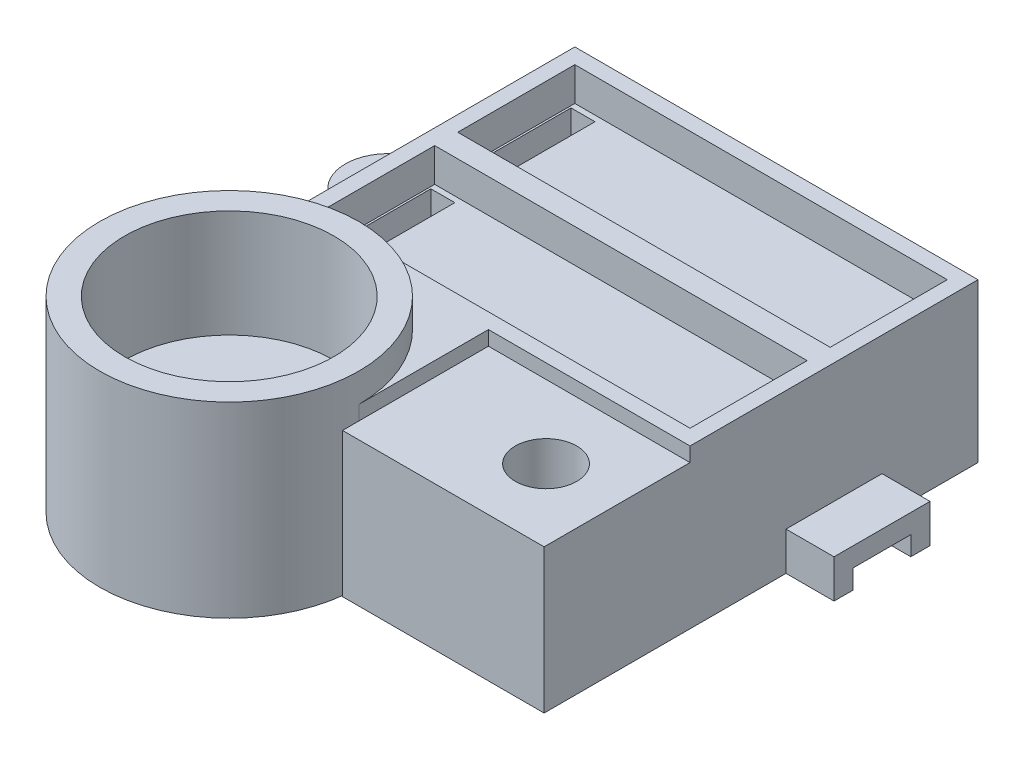
SolidWorks part; units mm, degrees
ref_plane "Front Plane" through (0, 0, 0) normal (0, 0, 1) x (1, 0, 0)
ref_plane "Top Plane" through (0, 0, 0) normal (0, 1, 0) x (1, 0, 0)
ref_plane "Right Plane" through (0, 0, 0) normal (1, 0, 0) x (0, 0, -1)
sketch "Sketch1" plane through (0, 0, 0) normal (0, 1, 0) x (1, 0, 0)
  line L1 (0, 0) -> (42, 0)
  line L2 (0, 0) -> (0, 30)
  line L3 (0, 30) -> (42, 30)
  line L4 (42, 0) -> (42, 30)
  dimension "D1" = 30
  dimension "D2" = 42
extrude "Boss-Extrude1" add sketch "Sketch1" along normal blind 10.5
sketch "Sketch2" plane through (0, 10.5, 0) normal (0, 1, 0) x (1, 0, 0)
  line L1 (1.6, 16.2) -> (40.4, 16.2)
  line L2 (1.6, 16.2) -> (1.6, 28.4)
  line L3 (1.6, 28.4) -> (40.4, 28.4)
  line L4 (40.4, 16.2) -> (40.4, 28.4)
  line L5 (0, 30) -> (0, 0) construction
  line L6 (42, 30) -> (0, 30) construction
  line L7 (0, 15) -> (42, 15)
  line L8 (42, 0) -> (42, 30) construction
  line L9 (1.6, 1.6) -> (40.4, 1.6)
  line L10 (40.4, 13.8) -> (40.4, 1.6)
  line L11 (1.6, 13.8) -> (40.4, 13.8)
  line L12 (1.6, 13.8) -> (1.6, 1.6)
  dimension "D1" = 12.2
  dimension "D2" = 1.6
  dimension "D3" = 38.8
  dimension "D4" = 1.6
extrude "Cut-Extrude1" cut sketch "Sketch2" against normal blind 3.5 contours L1 L4 L3 L2 | L11 L12 L9 L10
sketch "Sketch3" plane through (0, 7, 0) normal (0, 1, 0) x (1, 0, 0)
  line L0 (1.6, 16.2) -> (40.4, 16.2) construction
  line L1 (1.8, 27.8) -> (4.3, 27.8)
  line L2 (1.8, 27.8) -> (1.8, 16.8)
  line L3 (1.8, 16.8) -> (4.3, 16.8)
  line L4 (4.3, 27.8) -> (4.3, 16.8)
  line L5 (1.6, 16.2) -> (1.6, 28.4) construction
  line L6 (0, 15) -> (42, 15) construction
  line L7 (0, 30) -> (0, 0) construction
  line L8 (42, 0) -> (42, 30) construction
  line L9 (1.8, 13.2) -> (4.3, 13.2)
  line L10 (4.3, 2.2) -> (4.3, 13.2)
  line L11 (1.8, 2.2) -> (4.3, 2.2)
  line L12 (1.8, 2.2) -> (1.8, 13.2)
  point P4 (4.3, 22.3)
  dimension "D1" = 11
  dimension "D2" = 6.1
  dimension "D3" = 0.2
  dimension "D4" = 2.5
extrude "Cut-Extrude2" cut sketch "Sketch3" against normal blind 2.6
sketch "Sketch4" plane through (0, 4.4, 0) normal (0, 1, 0) x (1, 0, 0)
  line L0 (3.05, 27.8) -> (3.05, 2.2) construction
  line L1 (4.3, 27.8) -> (1.8, 27.8) construction
  line L2 (1.8, 2.2) -> (4.3, 2.2) construction
  line L3 (4.3, 27.8) -> (1.8, 27.8) construction
  line L4 (1.8, 22.3) -> (4.3, 22.3) construction
  line L5 (1.8, 27.8) -> (1.8, 16.8) construction
  line L6 (4.3, 16.8) -> (4.3, 27.8) construction
  line L7 (0, 15) -> (42, 15) construction
  line L8 (0, 30) -> (0, 0) construction
  line L9 (42, 0) -> (42, 30) construction
  line L10 (2.3, 26.05) -> (2.3, 18.55)
  line L11 (3.8, 26.05) -> (3.8, 18.55)
  line L12 (2.3, 11.45) -> (2.3, 3.95)
  line L13 (3.8, 11.45) -> (3.8, 3.95)
  circle A0 centre (3.05, 26.05) radius 0.75
  circle A1 centre (3.05, 23.8) radius 0.75
  circle A2 centre (3.05, 20.8) radius 0.75
  circle A3 centre (3.05, 18.55) radius 0.75
  circle A4 centre (3.05, 11.45) radius 0.75
  circle A5 centre (3.05, 9.2) radius 0.75
  circle A6 centre (3.05, 6.2) radius 0.75
  circle A7 centre (3.05, 3.95) radius 0.75
  dimension "D1" = 1.5
  dimension "D3" = 1.5
  dimension "D4" = 2.25
  dimension "D2" = 1.75
extrude "Cut-Extrude3" cut sketch "Sketch4" against normal through all contours A0 | A1 L11 A0 L10 | A1 | L10 A2 L11 A1 | A2 | L10 A3 L11 A2 | A3 | A4 | A5 L13 A4 L12 | A5 | L12 A6 L13 A5 | A6 | L12 A7 L13 A6 | A7
sketch "Sketch5" [suppressed] plane through (42, 0, 0) normal (1, 0, 0) x (0, 0, -1)
  line L0 (0, 9.5) -> (0, 0) construction
  line L1 (0, 0) -> (30, 0)
  line L2 (0, 0) -> (0, 7.5)
  line L3 (0, 7.5) -> (30, 7.5)
  line L4 (30, 0) -> (30, 7.5)
  line L5 (30, 9.5) -> (30, 0) construction
  line L6 (0, 9.5) -> (30, 9.5) construction
  line L8 (0, 0) -> (30, 0) construction
  dimension "D1" = 2
  dimension "D2" = 0
extrude "Boss-Extrude3" [suppressed] add sketch "Sketch5" along normal blind 25
sketch "Sketch6" [suppressed] plane through (0, 7.5, 0) normal (0, 1, 0) x (1, 0, 0)
  line L0 (42, 30) -> (42, 0) construction
  line L3 (67, 30) -> (42, 30) construction
  line L4 (67, 0) -> (42, 0) construction
  line L5 (55.2288, 0) -> (67, 0)
  line L6 (67, 0) -> (67, 30)
  line L7 (67, 30) -> (55.2288, 30)
  line L8 (42, 30) -> (0, 30) construction
  line L9 (0, 0) -> (42, 0) construction
  arc A1 (67, 15) -> (62, 30) centre (42, 15) ccw
  arc A2 (67, 15) -> (62, 0) centre (42, 15) cw
extrude "Cut-Extrude4" [suppressed] cut sketch "Sketch6" against normal through all
sketch "Sketch8" [suppressed] plane through (0, 7.5, 0) normal (0, 1, 0) x (1, 0, 0)
  line L0 (42, 30) -> (42, 0) construction
  line L2 (42, 30) -> (0, 30) construction
  line L3 (0, 0) -> (42, 0) construction
  line L4 (40.4, 16.2) -> (40.4, 28.4) construction
  line L5 (42, 15) -> (67, 15)
  arc A3 (62, 0) -> (62, 30) centre (42, 15) ccw construction
  circle A4 centre (54.5, 15) radius 3.5
  dimension "D1" = 7
  dimension "D2" = 1.6
extrude "Cut-Extrude5" [suppressed] cut sketch "Sketch8" against normal through all contours L5 A4 | L5 A4
sketch "Sketch13" plane through (0, 0, 0) normal (0, -1, 0) x (1, 0, 0)
  line L0 (42, 0) -> (42, -30)
  line L1 (0, 0) -> (42, 0) construction
  line L2 (42, -30) -> (0, -30) construction
  line L3 (0, -30) -> (0, 0) construction
  line L4 (0, -15) -> (42, -15) construction
  line L5 (1.6, -28.4) -> (40.4, -28.4)
  line L6 (1.6, -28.4) -> (1.6, -1.6)
  line L7 (1.6, -1.6) -> (40.4, -1.6)
  line L8 (40.4, -28.4) -> (40.4, -1.6)
  line L9 (37.55, -8.9) -> (42, -8.9)
  line L10 (37.55, -21.1) -> (42, -21.1)
  circle A2 centre (37.55, -4.45) radius 1.45
  circle A3 centre (37.55, -4.45) radius 4.45
  circle A4 centre (37.55, -25.55) radius 1.45
  circle A5 centre (37.55, -25.55) radius 4.45
  line M16 (42, 0) -> (0, 0)
  line M17 (0, 0) -> (0, -30)
  line M18 (0, -30) -> (42, -30)
  line M30 (42, -30) -> (42, 0)
  dimension "D6" = 2.9
  dimension "D7" = 8.9
  dimension "D8" = 4.45
  dimension "D1" = 42
  dimension "D2" = 1.6
  dimension "D3" = 1.6
  dimension "D4" = 1.6
  dimension "D5" = 1.6
  dimension "D9" = 4.45
extrude "Boss-Extrude6" add sketch "Sketch13" along normal blind 6 contours A5 L5 L8 A4 | A5 L8 L5 | L0 A5 M18 | L4 A5 L5 L6 M17 M18 | L7 A3 L8 A2 | L8 A3 L7 | A3 L0 M16 | L4 L6 L7 A3 M17 M16 | A3 L8 L9 L0 | L8 A5 L0 L10 | L4 L8 L10 L0 | L8 L4 L9 M30
sketch "Sketch15" plane through (0, 0, 0) normal (0, -1, 0) x (1, 0, 0)
  line L1 (0, 0) -> (0, -30) construction
  line L4 (-4.45, -10.55) -> (0, -10.55)
  line L5 (-4.45, -19.45) -> (0, -19.45)
  line L6 (0, -10.55) -> (0, -19.45)
  circle A0 centre (-4.45, -15) radius 4.45
  circle A1 centre (-4.45, -15) radius 1.5
  dimension "D1" = 8.9
  dimension "D2" = 3
  dimension "D3" = 4.45
extrude "Boss-Extrude7" add sketch "Sketch15" along normal blind 6 contours A0 A1 | A0 L6 L4 | A0 L5 L6
sketch "Sketch16" plane through (0, 0, 0) normal (0, 1, 0) x (1, 0, 0)
  line L0 (-4.45, 19.45) -> (0, 19.45)
  line L1 (0, 19.45) -> (0, 10.55)
  line L2 (0, 10.55) -> (-4.45, 10.55)
  circle A1 centre (-4.45, 15) radius 4.45
  circle M3 centre (-4.45, 15) radius 1.5
  arc M4 (-4.45, 19.45) -> (-4.45, 10.55) centre (-4.45, 15) ccw
  line M5 (-4.45, 10.55) -> (0, 10.55)
  line M6 (0, 10.55) -> (0, 19.45)
  line M7 (0, 19.45) -> (-4.45, 19.45)
  dimension "D2" = 8.9
extrude "Boss-Extrude8" add sketch "Sketch16" along normal blind 3 contours A1 L1 M7 | A1 M5 M6 | A1 M4 M3 | M3
sketch "Sketch17" plane through (0, 0, 0) normal (0, 0, 1) x (1, 0, 0)
  line L0 (31.5, 7.5) -> (31.5, -3) construction
  line L1 (21, -3) -> (42, -3)
  line L2 (21, -3) -> (21, 7.5)
  line L3 (21, 7.5) -> (42, 7.5)
  line L4 (42, -3) -> (42, 7.5)
  line L5 (42, 10.5) -> (42, -6) construction
  line L6 (21, 2.25) -> (42, 2.25) construction
  line L7 (21, 10.5) -> (21, -6) construction
  line L9 (0, 10.5) -> (42, 10.5) construction
  line L11 (42, -6) -> (0, -6) construction
  dimension "D1" = 10.5
  dimension "D2" = 3
  dimension "D3" = 3
  dimension "D4" = 21
extrude "Boss-Extrude9" add sketch "Sketch17" along normal blind 21
ref_plane "Plane1" through (0, 2.55, 0) normal (0, 1, 0) x (1, 0, 0)
sketch "Sketch23" [suppressed] plane through (0, 3, 0) normal (0, 1, 0) x (1, 0, 0)
  line L0 (0, 15) -> (-8.9, 15) construction
  line L1 (0, 30) -> (0, 0) construction
  line L2 (-12.5, 27.5) -> (0, 27.5)
  line L3 (-12.5, 2.5) -> (0, 2.5)
  line L5 (0, 27.5) -> (0, 2.5)
  arc A0 (-4.45, 19.45) -> (-4.45, 10.55) centre (-4.45, 15) ccw construction
  circle A2 centre (-12.5, 15) radius 12.5
  dimension "D1" = 25
  dimension "D2" = 12.5
extrude "Boss-Extrude12" [suppressed] add sketch "Sketch23" along normal blind 7.5
sketch "Sketch24" [suppressed] plane through (0, 10.5, 0) normal (0, 1, 0) x (1, 0, 0)
  circle A3 centre (-12.5, 15) radius 10.8
  dimension "D1" = 21.6
extrude "Cut-Extrude7" [suppressed] cut sketch "Sketch24" against normal blind 5
sketch "Sketch27" [suppressed] plane through (1.6, 0, 0) normal (1, 0, 0) x (0, 0, -1)
  line L0 (15, -3) -> (15, 0) construction
  line L1 (28.4, -3) -> (1.6, -3) construction
  line L2 (28.4, 0) -> (1.6, 0) construction
  line L3 (14, 0) -> (14, -1.5)
  line L4 (16, 0) -> (16, -1.5)
  line L5 (14, -1.5) -> (16, -1.5)
  line L6 (14, 0) -> (16, 0)
  dimension "D1" = 1
  dimension "D2" = 1
  dimension "D3" = 1.5
extrude "Cut-Extrude9" [suppressed] cut sketch "Sketch27" against normal blind 2.5
ref_plane "Plane2" [suppressed] through (0, 0, -15) normal (0, 0, 1) x (1, 0, 0)
sketch "Sketch31" [suppressed] plane through (0, 3, 0) normal (0, -1, 0) x (1, 0, 0)
  line L0 (-8.9, -15) -> (-25, -15) construction
  line L1 (-23.6647, -16) -> (-23.6647, -14)
  line L2 (-23.6647, -14) -> (-19.9868, -14)
  line L3 (-19.9868, -14) -> (-19.9868, -16)
  line L4 (-19.9868, -16) -> (-23.6647, -16)
  arc A0 (-4.45, -10.55) -> (-4.45, -19.45) centre (-4.45, -15) ccw construction
  circle A1 centre (-12.5, -15) radius 12.5 construction
  point P10 (-23.6647, -15)
  dimension "D1" = 2
extrude "Boss-Extrude15" [suppressed] add sketch "Sketch31" along normal blind 6
sketch "Sketch32" [suppressed] plane through (-19.9868, 0, 0) normal (1, 0, 0) x (0, 0, -1)
  line L0 (14, -3) -> (16, -3)
  line L1 (16, -3) -> (16, 3)
  line L2 (16, 3) -> (14, 3)
  line L3 (14, 3) -> (14, -3)
extrude "Boss-Extrude16" [suppressed] add sketch "Sketch32" along normal up to surface (11.2006 mm away)
sketch "Sketch33" [suppressed] plane through (0, 0, -16) normal (0, 0, -1) x (-1, 0, 0)
  line L0 (8.7862, -3) -> (23.6647, 3)
  line L1 (23.6647, 3) -> (23.6647, -3)
  line L2 (23.6647, -3) -> (8.7862, -3)
extrude "Cut-Extrude10" [suppressed] cut sketch "Sketch33" against normal blind 6
sketch "Sketch34" [suppressed] plane through (0, 10.5, 0) normal (0, 1, 0) x (1, 0, 0)
  line L2 (0, 27.5) -> (-12.5, 27.5)
  arc A0 (-12.5, 27.5) -> (-12.5, 2.5) centre (-12.5, 15) ccw
  circle A1 centre (-12.5, 15) radius 10.8
  circle A2 centre (-12.5, 15) radius 12.5
extrude "Boss-Extrude17" [suppressed] add sketch "Sketch34" along normal blind 14.8
sketch "Sketch35" plane through (0, 0, -30) normal (0, 0, -1) x (-1, 0, 0)
  line L0 (-15, 10.5) -> (-15, -6)
  line L1 (-42, 10.5) -> (0, 10.5) construction
  line L2 (0, -6) -> (-42, -6) construction
  line L3 (-42, 10.5) -> (-42, -6) construction
  line L4 (-15, 10.5) -> (-42, 10.5)
  line L7 (-42, 10.5) -> (-42, -9)
  line L8 (-42, -9) -> (-15, -9)
  line L9 (-15, -9) -> (-15, -6)
  dimension "D1" = 27
  dimension "D2" = 3
extrude "Boss-Extrude18" [suppressed] add sketch "Sketch35" along normal blind 27
sketch "Sketch36" [suppressed] plane through (0, 10.5, 0) normal (0, 1, 0) x (1, 0, 0)
  line L0 (15, 43.5) -> (42, 43.5) construction
  line L1 (15, 57) -> (15, 30) construction
  line L2 (42, 0) -> (42, 57) construction
  line L4 (15, 43.5) -> (15, 57)
  line L5 (15, 57) -> (42, 57)
  line L6 (42, 57) -> (42, 43.5)
  arc A2 (15, 43.5) -> (28.5, 57) centre (28.5, 43.5) cw
  arc A4 (42, 43.5) -> (28.5, 57) centre (28.5, 43.5) ccw
  line M7 (42, 0) -> (42, 57)
  line M8 (42, 57) -> (15, 57)
  line M9 (15, 57) -> (15, 30)
extrude "Cut-Extrude11" [suppressed] cut sketch "Sketch36" against normal blind 27 contours A2 L5 M9 | A4 M7 M8
sketch "Sketch37" [suppressed] plane through (0, 10.5, 0) normal (0, 1, 0) x (1, 0, 0)
  line L0 (15, 43.5) -> (42, 43.5) construction
  circle A0 centre (28.5, 43.5) radius 10.9
  dimension "D1" = 21.8
extrude "Cut-Extrude12" [suppressed] cut sketch "Sketch37" against normal blind 4.4
sketch "Sketch38" [suppressed] plane through (0, 6.1, 0) normal (0, 1, 0) x (1, 0, 0)
  line L0 (15, 43.5) -> (42, 43.5) construction
  line L1 (28.05, 41) -> (28.05, 46)
  line L2 (28.05, 41) -> (28.95, 41)
  line L3 (28.05, 46) -> (28.95, 46)
  line L4 (28.95, 41) -> (28.95, 46)
  line L5 (28.05, 41) -> (28.95, 46) construction
  line L6 (28.05, 46) -> (28.95, 41) construction
  line L7 (21.8, 41) -> (21.8, 46)
  line L8 (21.8, 46) -> (20.9, 46)
  line L9 (20.9, 46) -> (20.9, 41)
  line L10 (20.9, 41) -> (21.8, 41)
  line L11 (21.35, 46) -> (21.35, 41) construction
  line L12 (28.5, 46) -> (28.5, 41) construction
  circle A1 centre (21.35, 43.5) radius 1
  circle A2 centre (28.5, 43.5) radius 1
  point P5 (28.5, 43.5)
  point P6 (28.5, 43.5)
  point P14 (21.8, 43.5)
  dimension "D7" = 2
  dimension "D6" = 2
  dimension "D1" = 0.9
  dimension "D2" = 5
  dimension "D3" = 5
  dimension "D4" = 6.25
  dimension "D5" = 0.9
extrude "Cut-Extrude13" [suppressed] cut sketch "Sketch38" against normal blind 7.6 contours A1 L7 L8 L9 | L7 A1 | L9 A1 | L7 A1 L9 | A1 L9 L10 L7 | A2 L4 L3 L1 | L4 A2 L1 | L4 A2 | L1 A2 | A2 L1 L2 L4
sketch "Sketch40" [suppressed] plane through (0, 0, 0) normal (0, -1, 0) x (1, 0, 0)
  line L0 (22.35, -43.5) -> (22.35, -28.4)
  line L2 (15, -43.5) -> (42, -43.5) construction
  line L3 (1.6, -28.4) -> (34.1324, -28.4) construction
  line L4 (20.35, -43.5) -> (20.35, -28.4)
  line L5 (1.6, -28.4) -> (34.1324, -28.4) construction
  line L6 (27.5, -43.5) -> (27.5, -28.4)
  line L7 (29.5, -43.5) -> (29.5, -28.4)
  circle A0 centre (21.35, -43.5) radius 1 construction
  circle A1 centre (28.5, -43.5) radius 1 construction
sketch "Sketch41" [suppressed] plane through (0, 0, -28.4) normal (0, 0, 1) x (1, 0, 0)
  line L0 (20.35, 0) -> (20.35, -3)
  line L1 (1.6, -3) -> (34.1324, -3) construction
  line L2 (22.35, 0) -> (22.35, -3)
  line L3 (27.5, 0) -> (27.5, -3)
  line L4 (29.5, 0) -> (29.5, -3)
  line L5 (20.35, -1.5) -> (29.5, -1.5)
  line L6 (20.35, 0) -> (29.5, 0)
  line M2 (34.1324, 0) -> (1.6, 0)
extrude "Cut-Extrude14" [suppressed] cut sketch "Sketch41" against normal blind 15.1 contours L3 L5 L4 M2 | L0 L5 L2 M2
sketch "Sketch42" [suppressed] plane through (0, 10.5, 0) normal (0, 1, 0) x (1, 0, 0)
  circle A0 centre (28.5, 43.5) radius 13.5
  circle A1 centre (28.5, 43.5) radius 10.9
  circle M3 centre (28.5, 43.5) radius 10.9
  arc M13 (42, 43.5) -> (15, 43.5) centre (28.5, 43.5) ccw
extrude "Boss-Extrude19" [suppressed] add sketch "Sketch42" along normal blind 7 contours A0 M13 M3 | A1
sketch "Sketch43" plane through (0, 0, 0) normal (0, 0, 1) x (1, 0, 0)
  line L0 (21, 10.5) -> (21, -6)
  line L1 (0, 10.5) -> (42, 10.5) construction
  line L2 (42, -6) -> (0, -6) construction
  line L3 (-6, 10.5) -> (-6, -6)
  line L4 (-4.45, -6) -> (0, -6) construction
  line L5 (-6, 10.5) -> (21, 10.5)
  line L6 (-6, -6) -> (-6, -9)
  line L7 (-6, -9) -> (21, -9)
  line L8 (21, -9) -> (21, -6)
  dimension "D1" = 27
  dimension "D2" = 3
extrude "Boss-Extrude20" add sketch "Sketch43" along normal blind 27
sketch "Sketch44" plane through (0, 10.5, 0) normal (0, 1, 0) x (1, 0, 0)
  line L0 (-6, -13.5) -> (21, -13.5) construction
  line L1 (-6, -27) -> (-6, 0) construction
  line L2 (21, -27) -> (21, 0) construction
  line L3 (21, -27) -> (-6, -27) construction
  line L4 (-6, -13.5) -> (-6, -27)
  line L5 (-6, -27) -> (21, -27)
  line L6 (21, -27) -> (21, -13.5)
  line L7 (0, 0) -> (0, -27) construction
  line L8 (0, 0) -> (-6, 0)
  line L9 (-6, 0) -> (-6, -13.5)
  line L10 (-6, 0) -> (-6, -13.5)
  line L11 (0, 0) -> (0, -2.275)
  arc A0 (-6, -13.5) -> (7.5, -27) centre (7.5, -13.5) ccw
  arc A1 (21, -13.5) -> (7.5, -27) centre (7.5, -13.5) cw
  arc A2 (-6, -13.5) -> (0, -2.275) centre (7.5, -13.5) cw
  line M5 (0, 0) -> (-6, 0)
  line M6 (-6, 0) -> (-6, -27)
  line M7 (-6, -27) -> (21, -27)
  line M8 (21, -27) -> (21, 0)
extrude "Cut-Extrude15" cut sketch "Sketch44" against normal blind 27 contours A1 L5 M8 | A0 M6 M7 | A2 L11 M6 M5
sketch "Sketch45" plane through (0, 10.5, 0) normal (0, 1, 0) x (1, 0, 0)
  line L0 (21, -13.5) -> (-6, -13.5)
  circle A0 centre (7.5, -13.5) radius 10.9
  arc A1 (0, -2.275) -> (21, -13.5) centre (7.5, -13.5) ccw construction
  dimension "D1" = 21.8
extrude "Cut-Extrude16" cut sketch "Sketch45" against normal blind 8.2
sketch "Sketch46" plane through (0, 2.3, 0) normal (0, 1, 0) x (1, 0, 0)
  line L1 (6.85, -16.25) -> (6.85, -10.75)
  line L2 (6.85, -16.25) -> (8.15, -16.25)
  line L3 (6.85, -10.75) -> (8.15, -10.75)
  line L4 (8.15, -16.25) -> (8.15, -10.75)
  line L5 (6.85, -16.25) -> (8.15, -10.75) construction
  line L6 (6.85, -10.75) -> (8.15, -16.25) construction
  line L7 (0.6, -10.75) -> (0.6, -16.25)
  line L8 (0.6, -16.25) -> (-0.7, -16.25)
  line L9 (-0.7, -16.25) -> (-0.7, -10.75)
  line L10 (-0.7, -10.75) -> (0.6, -10.75)
  line L11 (-0.05, -10.75) -> (-0.05, -16.25) construction
  line L12 (7.5, -10.75) -> (7.5, -16.25) construction
  line L13 (15.7, -16.25) -> (15.7, -10.75)
  line L14 (14.4, -16.25) -> (15.7, -16.25)
  line L15 (14.4, -10.75) -> (14.4, -16.25)
  line L16 (15.7, -10.75) -> (14.4, -10.75)
  line L17 (-6, -13.5) -> (21, -13.5) construction
  circle A0 centre (-0.05, -13.5) radius 1.5
  circle A1 centre (7.5, -13.5) radius 1.5
  circle A2 centre (15.05, -13.5) radius 1.5
  arc A3 (0, -2.275) -> (21, -13.5) centre (7.5, -13.5) ccw construction
  point P5 (7.5, -13.5)
  point P31 (7.5, -13.5)
  dimension "D5" = 3
  dimension "D6" = 3
  dimension "D1" = 1.3
  dimension "D2" = 5.5
  dimension "D3" = 6.25
  dimension "D4" = 1.3
  dimension "D7" = 5.5
extrude "Cut-Extrude17" cut sketch "Sketch46" against normal through all contours A1 L4 L3 L1 | L4 A1 L1 | L4 A1 | A1 L1 L2 L4 | L1 A1 | A2 L13 | A2 L15 | L15 A2 L13 L16 | L13 A2 L15 L14
sketch "Sketch47" plane through (0, 0, 0) normal (0, -1, 0) x (1, 0, 0)
  line L0 (16.55, 13.5) -> (16.55, -1.6)
  line L2 (1.6, -1.6) -> (34.1324, -1.6) construction
  line L3 (9, 13.5) -> (9, -1.6)
  line L4 (1.6, -1.6) -> (34.1324, -1.6) construction
  line L5 (13.55, 13.5) -> (13.55, -1.6)
  line L6 (-6, 13.5) -> (21, 13.5) construction
  line L7 (6, 13.5) -> (6, -1.6)
  circle A0 centre (7.5, 13.5) radius 1.5 construction
  circle A1 centre (15.05, 13.5) radius 1.5 construction
sketch "Sketch48" plane through (0, 0, -1.6) normal (0, 0, -1) x (-1, 0, 0)
  line L2 (-1.6, -6) -> (-34.1324, -6) construction
  line L3 (-6.5, -6) -> (-15.65, -6)
  line L5 (-13.55, 0) -> (-13.55, -6)
  line L6 (-9, 0) -> (-9, -6)
  line L7 (-15.65, -3) -> (-6.5, -3)
  line L11 (-16.55, 0) -> (-6, 0)
  line L12 (-6, 0) -> (-6, -6)
  line L13 (-6, -6) -> (-6.5, -6)
  line L14 (-6.5, -3) -> (-6, -3)
  line L15 (-16.55, 0) -> (-16.55, -6)
  line L16 (-16.55, -6) -> (-15.65, -6)
  line L17 (-15.65, -3) -> (-16.55, -3)
  dimension "D1" = 3
extrude "Cut-Extrude18" cut sketch "Sketch48" against normal blind 15.1
sketch "Sketch49" plane through (0, 10.5, 0) normal (0, 1, 0) x (1, 0, 0)
  circle A0 centre (7.5, -13.5) radius 13.5
  circle A1 centre (7.5, -13.5) radius 10.9
extrude "Boss-Extrude21" add sketch "Sketch49" along normal blind 3
sketch "Sketch51" plane through (0, 0, 0) normal (0, 0, -1) x (-1, 0, 0)
  line L0 (4.45, -6) -> (8.9, -6) construction
  line L1 (-21, -9) -> (7.8273, -9)
  line L2 (-21, -9) -> (-21, -6)
  line L3 (-21, -6) -> (7.8273, -6)
  line L4 (7.8273, -9) -> (7.8273, -6)
extrude "Cut-Extrude20" cut sketch "Sketch51" against normal through all
sketch "Sketch52" plane through (42, 0, 0) normal (1, 0, 0) x (0, 0, -1)
  line L0 (15, -6) -> (18, -6) construction
  line L2 (30, -6) -> (0, -6) construction
  line L3 (15, -6) -> (12, -6) construction
  line L4 (12, -6) -> (18, -6)
  line L5 (18, -6) -> (18, -4)
  line L6 (18, -4) -> (12, -4)
  line L7 (12, -4) -> (12, -6)
  dimension "D1" = 3
  dimension "D2" = 3
  dimension "D3" = 2
extrude "Cut-Extrude21" cut sketch "Sketch52" against normal blind 10
sketch "Sketch53" plane through (42, 0, 0) normal (1, 0, 0) x (0, 0, -1)
  line L0 (12, -6) -> (10, -6)
  line L1 (28.4, -6) -> (1.6, -6) construction
  line L2 (10, -6) -> (10, -2)
  line L3 (10, -2) -> (20, -2)
  line L4 (20, -2) -> (20, -6)
  line L5 (30, -6) -> (18, -6) construction
  line L6 (12, -6) -> (12, -4)
  line L7 (12, -4) -> (18, -4)
  line L8 (18, -4) -> (18, -6)
  line L9 (18, -6) -> (20, -6)
  dimension "D1" = 2
  dimension "D2" = 2
  dimension "D3" = 2
extrude "Boss-Extrude22" add sketch "Sketch53" along normal blind 5
sketch "Sketch54" plane through (0, -6, 0) normal (0, -1, 0) x (1, 0, 0)
  line L0 (21, 13.5) -> (0, 13.5) construction
  line L1 (0, -10.55) -> (0, 13.5) construction
  circle A1 centre (0, 13.5) radius 1.5
  dimension "D1" = 3
extrude "Cut-Extrude22" cut sketch "Sketch54" against normal blind 3
sketch "Sketch55" plane through (0, 0, 0) normal (0, -1, 0) x (1, 0, 0)
  circle A0 centre (-4.45, -15) radius 1.5
  circle A1 centre (37.55, -4.45) radius 1.45
  circle A2 centre (37.55, -25.55) radius 1.45
extrude "Boss-Extrude23" add sketch "Sketch55" along normal mid plane 6
sketch "Sketch57" plane through (0, -3, 0) normal (0, -1, 0) x (1, 0, 0)
  line L0 (21, 21) -> (42, 21)
  line L1 (21, 0) -> (42, 0)
  line L2 (21, 0) -> (21, 21)
  line L5 (21, 21) -> (42, 21) construction
  line L6 (42, 21) -> (42, 0)
extrude "Boss-Extrude25" add sketch "Sketch57" along normal blind 3
sketch "Sketch58" plane through (0, 7.5, 0) normal (0, 1, 0) x (1, 0, 0)
  line L0 (21, -21) -> (42, -21)
  line L5 (21, 0) -> (42, 0) construction
  line L6 (21, -15.2) -> (42, -15.2)
  line L7 (21, -15.2) -> (21, -21)
  line L9 (42, -15.2) -> (42, -21)
  dimension "D1" = 15.2
extrude "Cut-Extrude23" cut sketch "Sketch58" against normal through all
sketch "Sketch59" plane through (0, 7.5, 0) normal (0, 1, 0) x (1, 0, 0)
  line L0 (42, -7.6) -> (21, -7.6) construction
  line L1 (42, -15.2) -> (42, 0) construction
  line L2 (21, -13.5) -> (21, 0) construction
  circle A0 centre (34.6, -7.6) radius 3.2
  point P8 (37.8, -7.6)
  dimension "D2" = 6.4
  dimension "D1" = 4.2
extrude "Cut-Extrude24" cut sketch "Sketch59" against normal mid plane 300
sketch "Sketch60" plane through (0, 7.5, 0) normal (0, 1, 0) x (1, 0, 0)
  line L0 (42, 0) -> (42, -15.2)
  line L1 (21, -15.2) -> (42, -15.2)
  line L2 (21, -15.2) -> (21, 0)
  line L3 (21, 0) -> (42, 0)
  line L5 (42, -7.6) -> (21, -7.6) construction
  circle A0 centre (34.6, -7.6) radius 3.2
  point P8 (0, 0)
  point P11 (0, 0)
  circle M5 centre (34.6, -7.6) radius 3.2
  line M7 (21, -15.2) -> (42, -15.2)
  line M8 (42, -15.2) -> (42, 0)
  line M9 (42, 0) -> (21, 0)
  line M10 (21, 0) -> (21, -13.5)
  line M13 (21, -13.5) -> (21, -15.2)
extrude "Boss-Extrude26" add sketch "Sketch60" along normal blind 1.5 contours L5 L0 M9 M10 M5 | L5 A0 L2 M8 M13 M7
sketch "Sketch61" plane through (0, 0, 0) normal (0, -1, 0) x (1, 0, 0)
  line L0 (1.6, -1.6) -> (34.1324, -1.6)
  line L1 (1.6, -1.6) -> (1.6, -28.4)
  line L2 (1.6, -28.4) -> (34.1324, -28.4)
  line L3 (40.4, -7.8676) -> (40.4, -22.1324)
  circle A0 centre (37.55, -4.45) radius 4.45
  circle A1 centre (37.55, -25.55) radius 4.45
  arc M1 (3.8, -11.45) -> (2.3, -11.45) centre (3.05, -11.45) cw
  line M2 (2.3, -11.45) -> (2.3, -3.95)
  arc M3 (2.3, -3.95) -> (3.8, -3.95) centre (3.05, -3.95) cw
  line M4 (3.8, -3.95) -> (3.8, -11.45)
  arc M5 (3.8, -26.05) -> (2.3, -26.05) centre (3.05, -26.05) cw
  line M6 (2.3, -26.05) -> (2.3, -18.55)
  arc M7 (2.3, -18.55) -> (3.8, -18.55) centre (3.05, -18.55) cw
  line M8 (3.8, -18.55) -> (3.8, -26.05)
  arc M9 (34.1324, -28.4) -> (40.4, -22.1324) centre (37.55, -25.55) cw
  line M10 (40.4, -22.1324) -> (40.4, -7.8676)
  arc M11 (40.4, -7.8676) -> (34.1324, -1.6) centre (37.55, -4.45) cw
  line M12 (34.1324, -1.6) -> (1.6, -1.6)
  line M13 (1.6, -1.6) -> (1.6, -28.4)
  line M14 (1.6, -28.4) -> (34.1324, -28.4)
extrude "Cut-Extrude25" cut sketch "Sketch61" against normal blind 3 contours M14 M9 M10 M11 M12 M13 M8 M5 M6 M7 M4 M1 M2 M3
equation "\"D1@Cut-Extrude9\"=2.5"
